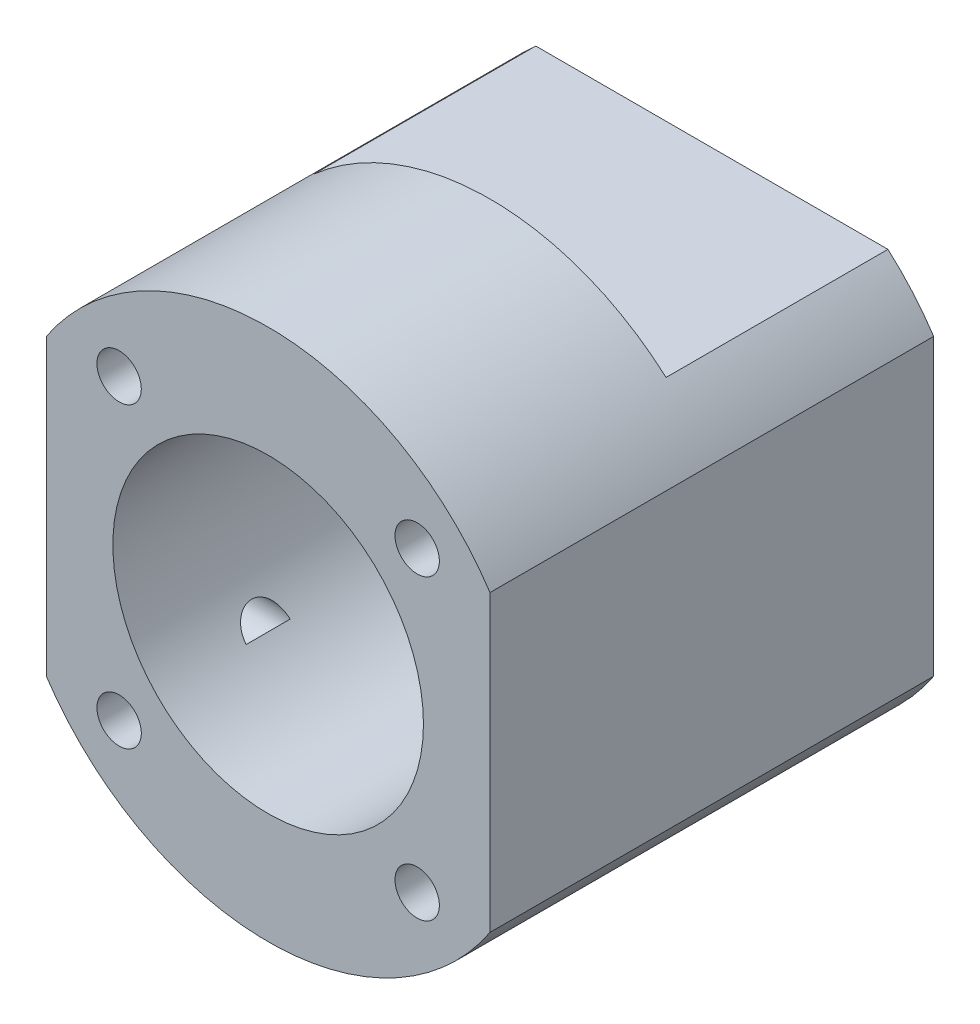
SolidWorks part; units mm, degrees
ref_plane "Piano frontale" through (0, 0, 0) normal (0, 0, 1) x (1, 0, 0)
ref_plane "Piano superiore" through (0, 0, 0) normal (0, 1, 0) x (1, 0, 0)
ref_plane "Piano destro" through (0, 0, 0) normal (1, 0, 0) x (0, 0, -1)
sketch "Schizzo1" plane through (0, 0, 0) normal (0, 0, 1) x (1, 0, 0)
  line L0 (0, 0) -> (-33.4653, 33.4653) construction
  line L1 (0, 0) -> (-48.3841, 0) construction
  line L2 (20, -13.2665) -> (20, 13.2665)
  line L3 (0, 0) -> (0, 37.5637) construction
  line L4 (-20, -13.2665) -> (-20, 13.2665)
  line L5 (20, -37.5637) -> (-20, 37.5637) construction
  line L6 (20, 37.5637) -> (-20, -37.5637) construction
  arc A0 (-20, -13.2665) -> (20, -13.2665) centre (0, 0) ccw
  arc A1 (20, 13.2665) -> (-20, 13.2665) centre (0, 0) ccw
  circle A2 centre (0, 0) radius 14
  dimension "D1" = 48
  dimension "D3" = 28
  dimension "D2" = 40
  dimension "D4" = 45
extrude "Estrusione-Estrusione1" add sketch "Schizzo1" against normal blind 40
sketch "Schizzo4" plane through (-20, 0, 0) normal (-1, 0, 0) x (0, 0, 1)
  line L0 (0, 0) -> (-40, 0) construction
  line L1 (0, 13.2665) -> (0, -13.2665) construction
  line L2 (-40, 13.2665) -> (-40, -13.2665) construction
  line L3 (-20, 13.2665) -> (-20, -13.2665) construction
  line L4 (-40, 13.2665) -> (0, 13.2665) construction
  line L5 (-40, -13.2665) -> (0, -13.2665) construction
  circle A0 centre (-10, 10) radius 2
  circle A1 centre (-10, -10) radius 2
  circle A2 centre (-30, -10) radius 2
  circle A3 centre (-30, 10) radius 2
  dimension "D3" = 4
  dimension "D1" = 10
  dimension "D2" = 10
extrude "Taglio-Estrusione1" cut sketch "Schizzo4" against normal blind 10
sketch "Schizzo5" plane through (0, 0, 0) normal (0, 0, 1) x (1, 0, 0)
  line L0 (0, 0) -> (0, 24) construction
  line L1 (0, 0) -> (-16.9706, 16.9706) construction
  line L2 (0, 0) -> (-20, 0) construction
  line L3 (-20, 13.2665) -> (-20, -13.2665) construction
  arc A0 (20, 13.2665) -> (-20, 13.2665) centre (0, 0) ccw construction
  circle A1 centre (0, 0) radius 19 construction
  circle A2 centre (-13.435, 13.435) radius 2
  circle A3 centre (13.435, 13.435) radius 2
  circle A4 centre (13.435, -13.435) radius 2
  circle A5 centre (-13.435, -13.435) radius 2
  point P11 (-13.435, 13.435)
  dimension "D2" = 38
  dimension "D3" = 4
  dimension "D1" = 45
extrude "Taglio-Estrusione2" cut sketch "Schizzo5" against normal blind 10
sketch "Schizzo6" plane through (0, 0, -40) normal (0, 0, -1) x (-1, 0, 0)
  line L0 (0, 0) -> (20, 0) construction
  line L1 (-15.8745, 18) -> (16.1288, 18)
  line L2 (-15.8745, 18) -> (-15.8745, 25.881)
  line L3 (-15.8745, 25.881) -> (16.1288, 25.881)
  line L4 (16.1288, 18) -> (16.1288, 25.881)
  line L5 (20, 13.2665) -> (20, -13.2665) construction
  line L6 (16.1288, -18) -> (16.1288, -25.881)
  line L7 (-15.8745, -25.881) -> (16.1288, -25.881)
  line L8 (-15.8745, -18) -> (-15.8745, -25.881)
  line L9 (-15.8745, -18) -> (16.1288, -18)
  arc A0 (20, 13.2665) -> (-20, 13.2665) centre (0, 0) ccw construction
  dimension "D1" = 18
extrude "Taglio-Estrusione3" cut sketch "Schizzo6" against normal blind 20
